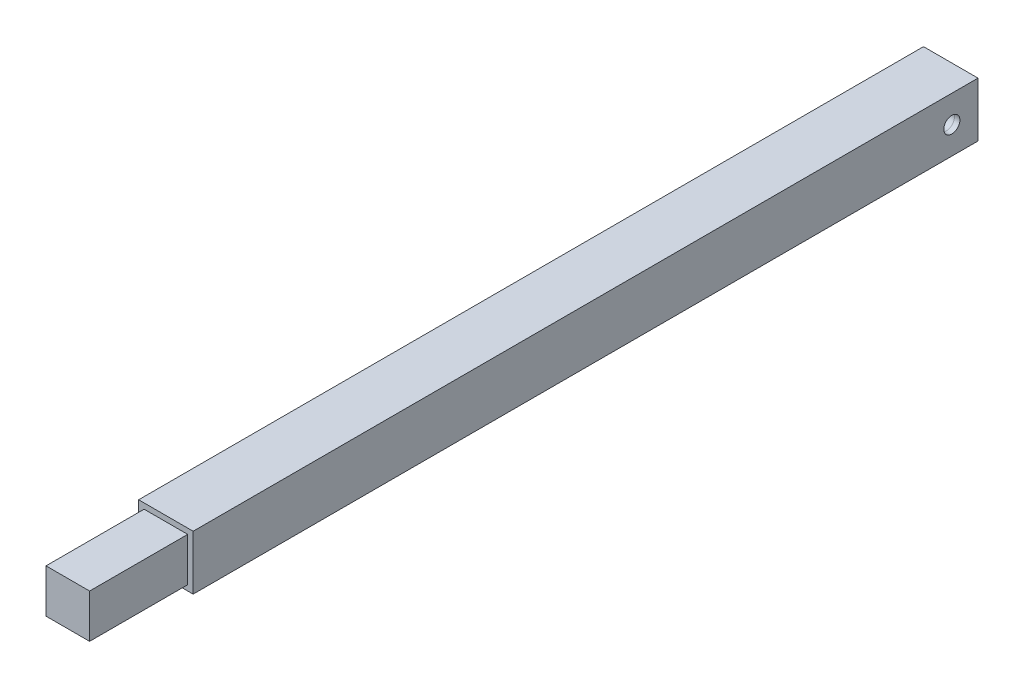
SolidWorks part; units mm, degrees
ref_plane "Front Plane" through (0, 0, 0) normal (0, 0, 1) x (1, 0, 0)
ref_plane "Top Plane" through (0, 0, 0) normal (0, 1, 0) x (1, 0, 0)
ref_plane "Right Plane" through (0, 0, 0) normal (1, 0, 0) x (0, 0, -1)
sketch "Sketch1" plane through (0, 0, 0) normal (0, 0, 1) x (1, 0, 0)
  line L0 (-12.7, 12.7) -> (12.7, 12.7)
  line L1 (-15.875, 15.875) -> (15.875, 15.875)
  line L2 (-15.875, 15.875) -> (-15.875, -15.875)
  line L3 (-15.875, -15.875) -> (15.875, -15.875)
  line L4 (15.875, 15.875) -> (15.875, -15.875)
  line L5 (12.7, 12.7) -> (12.7, -12.7)
  line L6 (-12.7, -12.7) -> (12.7, -12.7)
  line L7 (-12.7, 12.7) -> (-12.7, -12.7)
  dimension "D1" = 31.75
  dimension "D2" = 31.75
  dimension "D3" = 15.875
  dimension "D4" = 15.875
  dimension "D5" = 3.175
extrude "Extrude1" add sketch "Sketch1" along normal blind 457.2
sketch "Sketch2" plane through (0, 0, 457.2) normal (0, 0, 1) x (1, 0, 0)
  line L1 (-12.7, 12.7) -> (12.7, 12.7)
  line L2 (-12.7, 12.7) -> (-12.7, -12.7)
  line L3 (-12.7, -12.7) -> (12.7, -12.7)
  line L4 (12.7, 12.7) -> (12.7, -12.7)
extrude "Extrude2" add sketch "Sketch2" along normal blind 57.15
sketch "Sketch4" plane through (0, 0, 0) normal (0, 0, -1) x (-1, 0, 0)
  line L1 (-12.7, 12.7) -> (12.7, 12.7)
  line L2 (-12.7, 12.7) -> (-12.7, -12.7)
  line L3 (-12.7, -12.7) -> (12.7, -12.7)
  line L4 (12.7, 12.7) -> (12.7, -12.7)
extrude "Extrude4" add sketch "Sketch4" against normal blind 31.75 separate body
sketch "Sketch3" plane through (-15.875, 0, 0) normal (-1, 0, 0) x (0, 0, 1)
  circle A0 centre (15.24, 0) radius 4.699
  dimension "D1" = 9.398
  dimension "D2" = 15.24
  dimension "D3" = 15.875
extrude "Cut-Extrude3" cut sketch "Sketch3" against normal through all
sketch "Sketch5" plane through (0, 0, 0) normal (0, 0, -1) x (-1, 0, 0)
  circle A0 centre (0, 0) radius 1.0795
  dimension "D1" = 2.159
  dimension "D2" = 12.7
  dimension "D3" = 12.7
extrude "Cut-Extrude4" cut sketch "Sketch5" against normal blind 15.24
